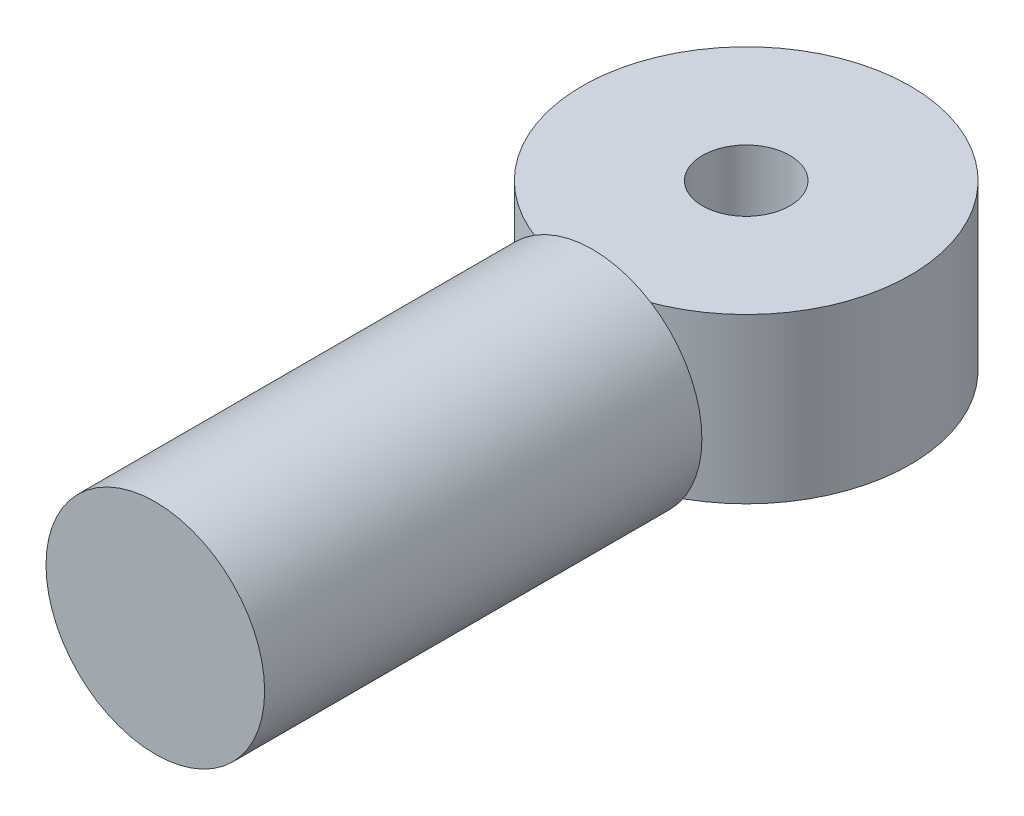
SolidWorks part; units mm, degrees
ref_plane "Front Plane" through (0, 0, 0) normal (0, 0, 1) x (1, 0, 0)
ref_plane "Top Plane" through (0, 0, 0) normal (0, 1, 0) x (1, 0, 0)
ref_plane "Right Plane" through (0, 0, 0) normal (1, 0, 0) x (0, 0, -1)
sketch "Sketch2" plane through (0, 0, 0) normal (0, 0, 1) x (1, 0, 0)
  circle A0 centre (0, 0) radius 10
  dimension "D1" = 20
extrude "Boss-Extrude1" add sketch "Sketch2" along normal blind 40
sketch "Sketch4" plane through (0, 0, 0) normal (0, 1, 0) x (1, 0, 0)
  line L0 (0, 0) -> (-1.8343, 29.9439)
  circle A0 centre (-0.9172, 14.9719) radius 15
  circle A1 centre (-0.9172, 14.9719) radius 4
  dimension "D1" = 30
extrude "Boss-Extrude2" add sketch "Sketch4" along normal mid plane 15 contours A1 | A0
